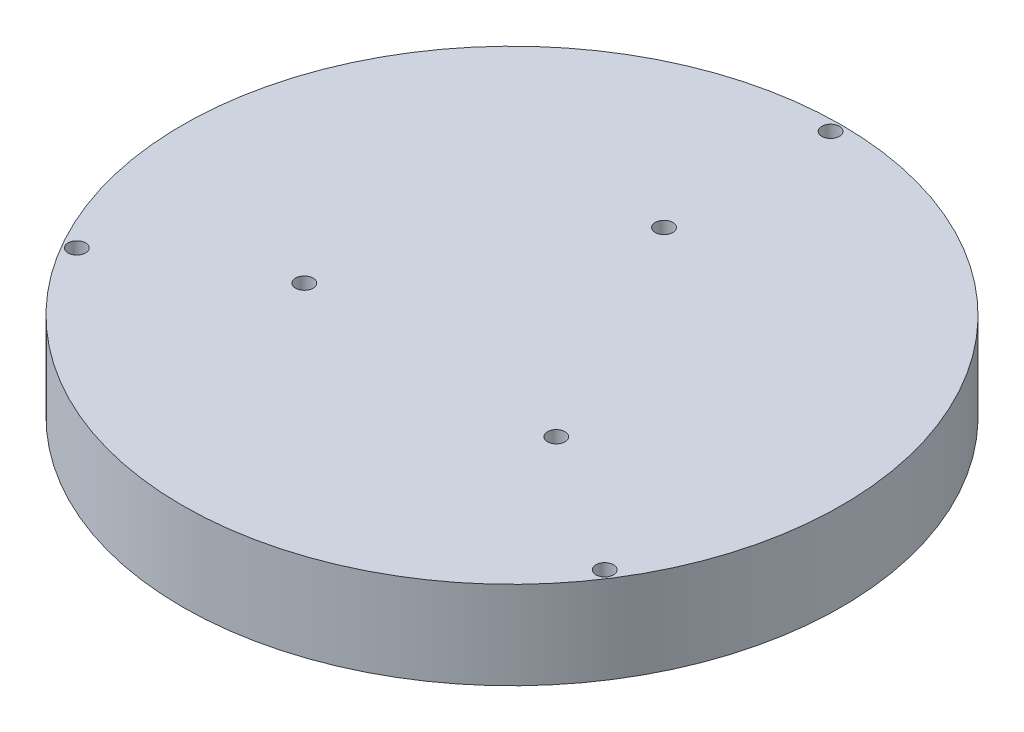
SolidWorks part; units mm, degrees
ref_plane "Front Plane" through (0, 0, 0) normal (0, 0, 1) x (1, 0, 0)
ref_plane "Top Plane" through (0, 0, 0) normal (0, 1, 0) x (1, 0, 0)
ref_plane "Right Plane" through (0, 0, 0) normal (1, 0, 0) x (0, 0, -1)
sketch "Sketch2" plane through (0, 0, 0) normal (0, 1, 0) x (1, 0, 0)
  circle A0 centre (0, 0) radius 37.5
  dimension "D1" = 75
sketch "Sketch3" plane through (0, 0, 0) normal (0, 1, 0) x (1, 0, 0)
  line L0 (0, 0) -> (33.4495, -21.8261) construction
  line L1 (0, 0) -> (-34.641, -20) construction
  circle A0 centre (0, 17.3) radius 1
  circle A1 centre (0, 36.25) radius 1
  circle A2 centre (14.4884, -9.4538) radius 1
  circle A3 centre (30.3587, -19.8093) radius 1
  circle A4 centre (-14.9822, -8.65) radius 1
  circle A5 centre (-31.3934, -18.125) radius 1
  circle A6 centre (0, 0) radius 37.5
  dimension "D1" = 2
  dimension "D2" = 17.3
  dimension "D3" = 36.25
  dimension "D4" = 17.3
  dimension "D5" = 36.25
  dimension "D6" = 17.3
  dimension "D7" = 36.25
extrude "Boss-Extrude2" add sketch "Sketch3" along normal blind 10
